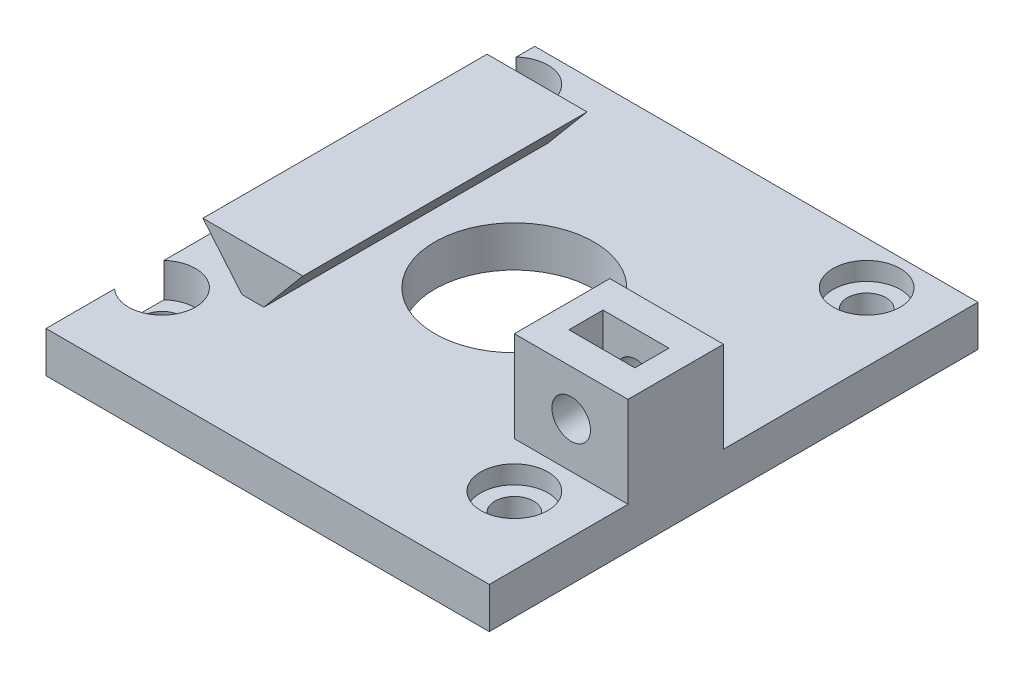
SolidWorks part; units mm, degrees
ref_plane "Alzado" through (0, 0, 0) normal (0, 0, 1) x (1, 0, 0)
ref_plane "Planta" through (0, 0, 0) normal (0, 1, 0) x (1, 0, 0)
ref_plane "Vista lateral" through (0, 0, 0) normal (1, 0, 0) x (0, 0, -1)
sketch "Croquis1" plane through (0, 0, 0) normal (0, 1, 0) x (1, 0, 0)
  line L5 (21.5, -23.7051) -> (-17.5, -23.7051)
  line L6 (21.5, -23.7051) -> (21.5, 19.2949)
  line L7 (15.5, -15.5) -> (-15.5, -15.5) construction
  line L8 (15.5, -15.5) -> (15.5, 15.5) construction
  line L9 (15.5, 15.5) -> (-15.5, 15.5) construction
  line L10 (-15.5, -15.5) -> (-15.5, 15.5) construction
  line L11 (15.5, -15.5) -> (-15.5, 15.5) construction
  line L12 (15.5, 15.5) -> (-15.5, -15.5) construction
  line L13 (21.5, 19.2949) -> (-17.5, 19.2949)
  line L14 (-17.5, -23.7051) -> (-17.5, 19.2949)
  line L15 (21.5, -23.7051) -> (-17.5, 19.2949) construction
  line L16 (21.5, 19.2949) -> (-17.5, -23.7051) construction
  circle A0 centre (0, 0) radius 7
  circle A1 centre (-15.5, 15.5) radius 1.7
  circle A2 centre (15.5, 15.5) radius 1.7
  circle A3 centre (-15.5, -15.5) radius 1.7
  circle A4 centre (15.5, -15.5) radius 1.7
  point P0 (0, 0)
  point P2 (0, 0)
  point P6 (0, 0)
  dimension "D4" = 3.4
  dimension "D5" = 14
  dimension "D6" = 17.5
  dimension "D1" = 39
  dimension "D2" = 43
  dimension "D3" = 31
extrude "Saliente-Extruir1" add sketch "Croquis1" along normal blind 3.6
sketch "Croquis2" plane through (0, 3.6, 0) normal (0, 1, 0) x (1, 0, 0)
  circle A0 centre (-15.5, 15.5) radius 2.95
  circle A1 centre (15.5, 15.5) radius 2.95
  circle A2 centre (-15.5, -15.5) radius 2.95
  circle A3 centre (15.5, -15.5) radius 2.95
  dimension "D1" = 5.9
extrude "Cortar-Extruir1" cut sketch "Croquis2" against normal blind 1.6
sketch "Croquis3" plane through (0, 3.6, 0) normal (0, 1, 0) x (1, 0, 0)
  line L0 (21.5, -23.7051) -> (21.5, 19.2949) construction
  line L1 (21.5, -11.5) -> (11.5, -11.5)
  line L2 (21.5, -11.5) -> (21.5, -3.1)
  line L3 (21.5, -3.1) -> (11.5, -3.1)
  line L4 (11.5, -11.5) -> (11.5, -3.1)
  line L5 (21.5, -11.5) -> (11.5, -3.1) construction
  line L6 (21.5, -3.1) -> (11.5, -11.5) construction
  point P0 (16.5, -7.3)
  dimension "D1" = 3.1
  dimension "D2" = 8.4
  dimension "D3" = 10
extrude "Saliente-Extruir2" add sketch "Croquis3" along normal blind 8
sketch "Croquis4" plane through (0, 0, 11.5) normal (0, 0, 1) x (1, 0, 0)
  line L0 (21.5, 11.6) -> (21.5, 3.6) construction
  line L1 (11.5, 11.6) -> (21.5, 11.6) construction
  circle A0 centre (16.5, 7.6) radius 1.7
  dimension "D1" = 3.4
  dimension "D2" = 5
  dimension "D3" = 4
extrude "Cortar-Extruir2" cut sketch "Croquis4" against normal blind 11
ref_plane "Plano1" through (0, 0, 7.3) normal (0, 0, 1) x (1, 0, 0)
sketch "Croquis5" plane through (0, 0, 7.3) normal (0, 0, 1) x (1, 0, 0)
  line L0 (13.5988, 9.275) -> (13.5988, 15.925)
  line L1 (13.5988, 9.275) -> (13.5988, 5.925)
  line L2 (13.5988, 5.925) -> (16.5, 4.25)
  line L3 (16.5, 4.25) -> (19.4012, 5.925)
  line L4 (19.4012, 5.925) -> (19.4012, 9.275)
  line L5 (19.4012, 9.275) -> (16.5, 10.95) construction
  line L6 (16.5, 10.95) -> (13.5988, 9.275) construction
  line L7 (13.5988, 15.925) -> (19.4012, 15.925)
  line L8 (19.4012, 15.925) -> (19.4012, 9.275)
  line L9 (11.5, 11.6) -> (11.5, 3.6) construction
  circle A0 centre (16.5, 7.6) radius 3.35 construction
  dimension "D1" = 6.7
  dimension "D2" = 10
extrude "Cortar-Extruir3" cut sketch "Croquis5" against normal blind 1.5 and the other way blind 1.5
sketch "Croquis6" plane through (0, 0, 0) normal (0, 0, 1) x (1, 0, 0)
  line L0 (-10.5, 2.4563) -> (-14.9, 7.7)
  line L1 (-14.9, 7.7) -> (-6.1, 7.7)
  line L2 (-6.1, 7.7) -> (-10.5, 2.4563)
  line L3 (-17.5, 3.6) -> (21.5, 3.6) construction
  dimension "D1" = 8.8
  dimension "D2" = 4.1
  dimension "D3" = 50
  dimension "D4" = 50
  dimension "D5" = 10.5
extrude "Saliente-Extruir3" add sketch "Croquis6" along normal blind 12.5 and the other way blind 12.5
sketch "Croquis7" plane through (0, 3.6, 0) normal (0, 1, 0) x (1, 0, 0)
  line L0 (-17.5, -13.3315) -> (-17.5, -17.6685) construction
  line L1 (-17.5, 17.6685) -> (-17.5, 13.3315) construction
  line L2 (-17.5, -13.3315) -> (-17.5, -17.6685)
  line L3 (-17.5, 17.6685) -> (-17.5, 13.3315)
  arc A0 (-17.5, -17.6685) -> (-17.5, -13.3315) centre (-15.5, -15.5) ccw construction
  arc A1 (-17.5, 13.3315) -> (-17.5, 17.6685) centre (-15.5, 15.5) ccw construction
  arc A2 (-17.5, -17.6685) -> (-17.5, -13.3315) centre (-15.5, -15.5) ccw
  arc A3 (-17.5, 13.3315) -> (-17.5, 17.6685) centre (-15.5, 15.5) ccw
extrude "Cortar-Extruir4" cut sketch "Croquis7" against normal blind 3
